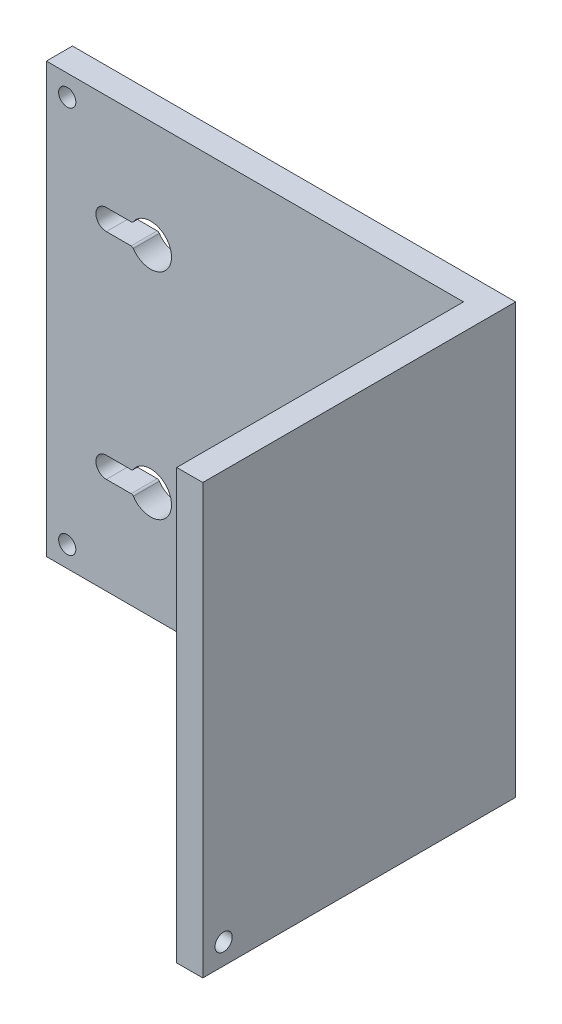
SolidWorks part; units mm, degrees
ref_plane "Front Plane" through (0, 0, 0) normal (0, 0, 1) x (1, 0, 0)
ref_plane "Top Plane" through (0, 0, 0) normal (0, 1, 0) x (1, 0, 0)
ref_plane "Right Plane" through (0, 0, 0) normal (1, 0, 0) x (0, 0, -1)
sketch "Sketch1" plane through (0, 0, 0) normal (0, 0, 1) x (1, 0, 0)
  line L1 (0, 0) -> (85, 0)
  line L2 (0, 0) -> (0, -82.3)
  line L3 (0, -82.3) -> (85, -82.3)
  line L4 (85, 0) -> (85, -82.3)
  dimension "D1" = 85
  dimension "D2" = 82.3
extrude "Boss-Extrude1" add sketch "Sketch1" along normal blind 60
sketch "Sketch2" plane through (0, -82.3, 0) normal (0, -1, 0) x (1, 0, 0)
  line L0 (85, 60) -> (85, 0) construction
  line L1 (0, 60) -> (80, 60)
  line L2 (0, 60) -> (0, 5)
  line L3 (0, 5) -> (80, 5)
  line L4 (80, 60) -> (80, 5)
  line L5 (0, 0) -> (85, 0) construction
  dimension "D1" = 5
  dimension "D2" = 5
extrude "Cut-Extrude1" cut sketch "Sketch2" against normal through all
sketch "Sketch3" plane through (0, 0, 5) normal (0, 0, 1) x (1, 0, 0)
  line L0 (0, -41.15) -> (80, -41.15) construction
  line L1 (0, 0) -> (0, -82.3) construction
  line L2 (80, 0) -> (80, -82.3) construction
  line L3 (40, -82.3) -> (40, -41.15) construction
  line L4 (0, -82.3) -> (80, -82.3) construction
  line L5 (40, -61.725) -> (0, -61.725) construction
  line L6 (20, -61.725) -> (11.5, -61.725) construction
  line L7 (20, -63.725) -> (11.5, -63.725) construction
  line L8 (20, -59.725) -> (11.5, -59.725) construction
  line L9 (16.5359, -63.725) -> (11.5, -63.725)
  line L10 (11.5, -63.725) -> (16.5359, -59.725) construction
  line L11 (16.5359, -59.725) -> (11.5, -59.725)
  circle A0 centre (20, -61.725) radius 4 construction
  arc A1 (20, -63.725) -> (20, -59.725) centre (20, -61.725) ccw construction
  arc A2 (11.5, -59.725) -> (11.5, -63.725) centre (11.5, -61.725) ccw construction
  arc A3 (16.5359, -63.725) -> (16.5359, -59.725) centre (20, -61.725) ccw
  arc A4 (11.5, -63.725) -> (11.5, -59.725) centre (11.5, -61.725) cw
  point P14 (15.75, -61.725)
  dimension "D1" = 8
  dimension "D3" = 2
  dimension "D2" = 8.5
extrude "Cut-Extrude2" cut sketch "Sketch3" against normal blind 50
fillet "Fillet1" radius 0.5 2 edges at (16.5359, -59.725, 2.5) (16.5359, -63.725, 2.5)
ref_plane "Plane1" through (0, -41.15, 0) normal (0, -1, 0) x (-1, 0, 0)
mirror "Mirror1" about plane through (0, -41.15, 0) normal (0, -1, 0) of "Cut-Extrude2", "Fillet1"
sketch "Sketch4" plane through (85, 0, 0) normal (1, 0, 0) x (0, 0, -1)
  line L0 (-60, -82.3) -> (0, -82.3) construction
  line L1 (-60, -82.3) -> (-60, 0) construction
  circle A0 centre (-56, -78.3) radius 1.65
  dimension "D1" = 3.3
  dimension "D2" = 4
  dimension "D3" = 4
extrude "Cut-Extrude3" cut sketch "Sketch4" against normal blind 20
sketch "Sketch5" plane through (0, 0, 0) normal (0, 0, -1) x (-1, 0, 0)
  line L0 (-4, 0) -> (-4, -82.3) construction
  line L1 (-85, 0) -> (0, 0) construction
  line L2 (0, -82.3) -> (-85, -82.3) construction
  line L3 (0, 0) -> (0, -82.3) construction
  circle A0 centre (-4, -4) radius 1.65
  circle A1 centre (-4, -78.3) radius 1.65
  dimension "D1" = 3.3
  dimension "D3" = 4
  dimension "D2" = 4
  dimension "D4" = 4
extrude "Cut-Extrude4" cut sketch "Sketch5" against normal blind 20
